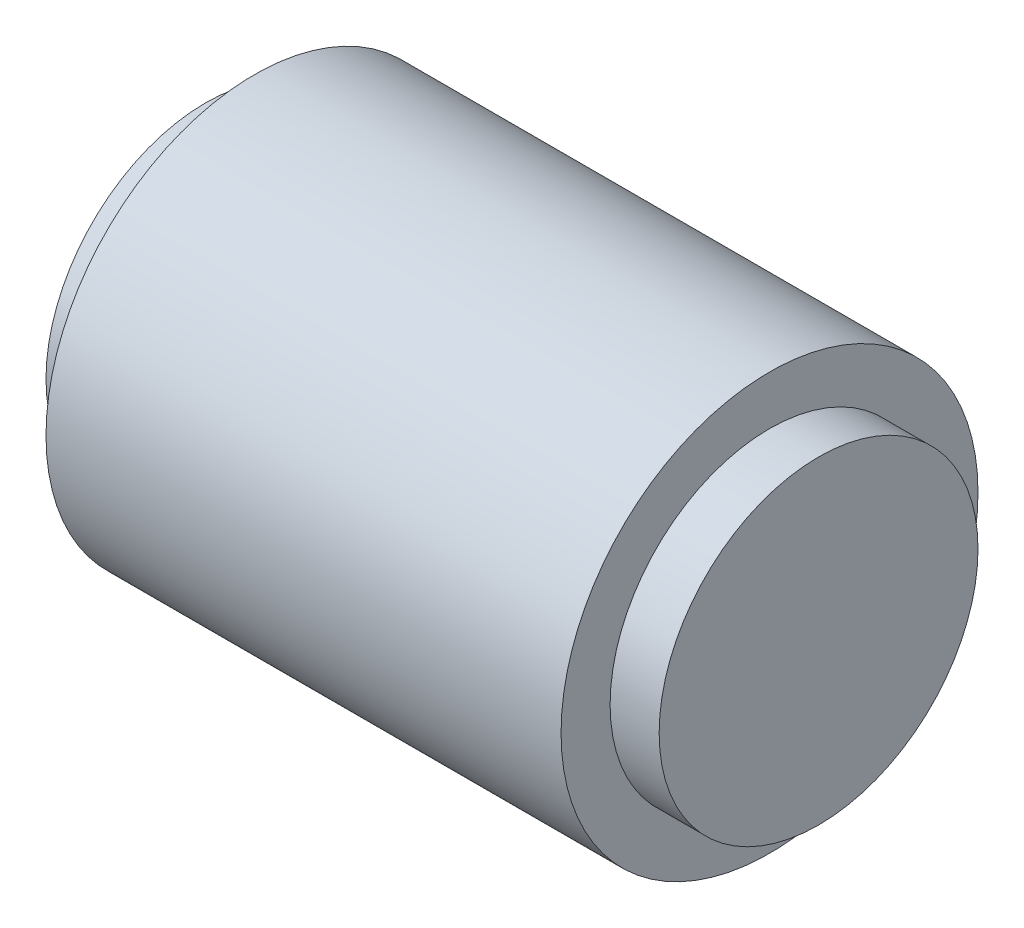
SolidWorks part; units mm, degrees
ref_plane "Face" through (0, 0, 0) normal (0, 0, 1) x (1, 0, 0)
ref_plane "Dessus" through (0, 0, 0) normal (0, 1, 0) x (1, 0, 0)
ref_plane "Droite" through (0, 0, 0) normal (1, 0, 0) x (0, 0, -1)
sketch "Esquisse1" plane through (0, 0, 0) normal (0, 0, 1) x (1, 0, 0)
  line L0 (-25, 0) -> (0, 0)
  line L1 (0, 0) -> (0, -6.5)
  line L2 (-2, -8.5) -> (-23, -8.5)
  line L3 (-25, -6.5) -> (-25, 0)
  line L4 (35.066, 0) -> (-50.1097, 0) construction
  line L5 (-23, -8.5) -> (-23, -6.5)
  line L6 (-23, -6.5) -> (-25, -6.5)
  line L9 (-2, -8.5) -> (-2, -6.5)
  line L10 (-2, -6.5) -> (0, -6.5)
revolve "Révolution1" add sketch "Esquisse1" angle 360 about L4
sketch "Esquisse2" plane through (0, 0, 0) normal (0, 1, 0) x (1, 0, 0)
  line L0 (-25, 0) -> (0, 0) construction
  circle A0 centre (-12.5, 0) radius 4.7
  dimension "D1" = 9.4
extrude "Enlèv. mat.-Extru.1" cut sketch "Esquisse2" against normal up to next
